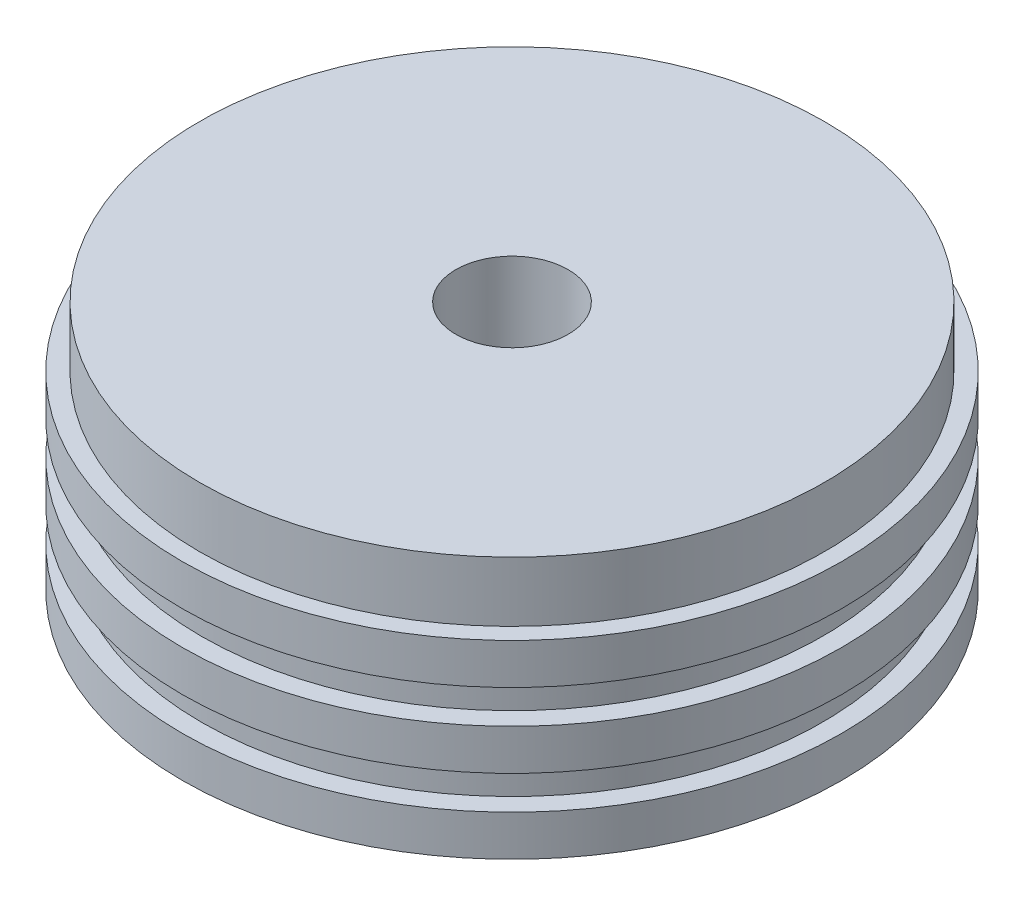
SolidWorks part; units mm, degrees
material "6061-T6 (SS)"
ref_plane "Front Plane" through (0, 0, 0) normal (0, 0, 1) x (1, 0, 0)
ref_plane "Top Plane" through (0, 0, 0) normal (0, 1, 0) x (1, 0, 0)
ref_plane "Right Plane" through (0, 0, 0) normal (1, 0, 0) x (0, 0, -1)
sketch "Sketch8" plane through (0, 0, 0) normal (0, 0, 1) x (1, 0, 0)
  line L0 (0, 0) -> (0, 26.416)
  line L1 (0, 26.416) -> (-33.0835, 26.416)
  line L2 (-33.0835, 26.416) -> (-33.0835, 20.066)
  line L3 (-33.0835, 20.066) -> (-34.8996, 20.066)
  line L4 (-34.8996, 20.066) -> (-34.8996, 15.748)
  line L5 (-34.8996, 15.748) -> (-32.8676, 15.748)
  line L7 (-32.8676, 7.874) -> (-34.8996, 7.874)
  line L8 (-34.8996, 7.874) -> (-34.8996, 12.192)
  line L11 (-32.8676, 4.318) -> (-34.8996, 4.318)
  line L12 (-34.8996, 4.318) -> (-34.8996, 0)
  line L13 (-34.8996, 0) -> (0, 0)
  line L14 (-34.8996, 12.192) -> (-32.8676, 12.192)
  line L15 (-32.8676, 15.748) -> (-32.8676, 12.192)
  line L16 (-32.8676, 7.874) -> (-32.8676, 4.318)
  dimension "D1" = 6.35
  dimension "D2" = 34.8996
  dimension "D3" = 32.8676
  dimension "D4" = 3.556
  dimension "D5" = 3.556
  dimension "D6" = 4.318
  dimension "D7" = 4.318
  dimension "D8" = 4.318
  dimension "D9" = 33.0835
revolve "Revolve1" add sketch "Sketch8" angle 360 about L0
hole_wizard "1/4-18 NPSM Tapped Hole1" positions "Sketch9" profile "Sketch10" tap size "1/4-18 NPSM" standard "ANSI Inch" end condition through all
sketch "Sketch9" plane through (0, 0, 0) normal (0, -1, 0) x (-1, 0, 0)
  point P0 (0, 0)
sketch "Sketch10" plane through (0, 0, 0) normal (1, 0, 0) x (0, 0, -1)
  line L0 (0, 0) -> (0, 26.416)
  line L1 (0, 26.416) -> (5.9436, 26.416)
  line L2 (5.9436, 26.416) -> (5.9436, 0)
  line L5 (5.9436, 0) -> (0, 0)
  line L11 (0, -6.35) -> (0, 107.95) construction
  dimension "Thru Tap Drill Dia." = 11.8872
  dimension "Thru Tap Drill Depth" = 26.416
cosmetic thread "Hole Thread1"
